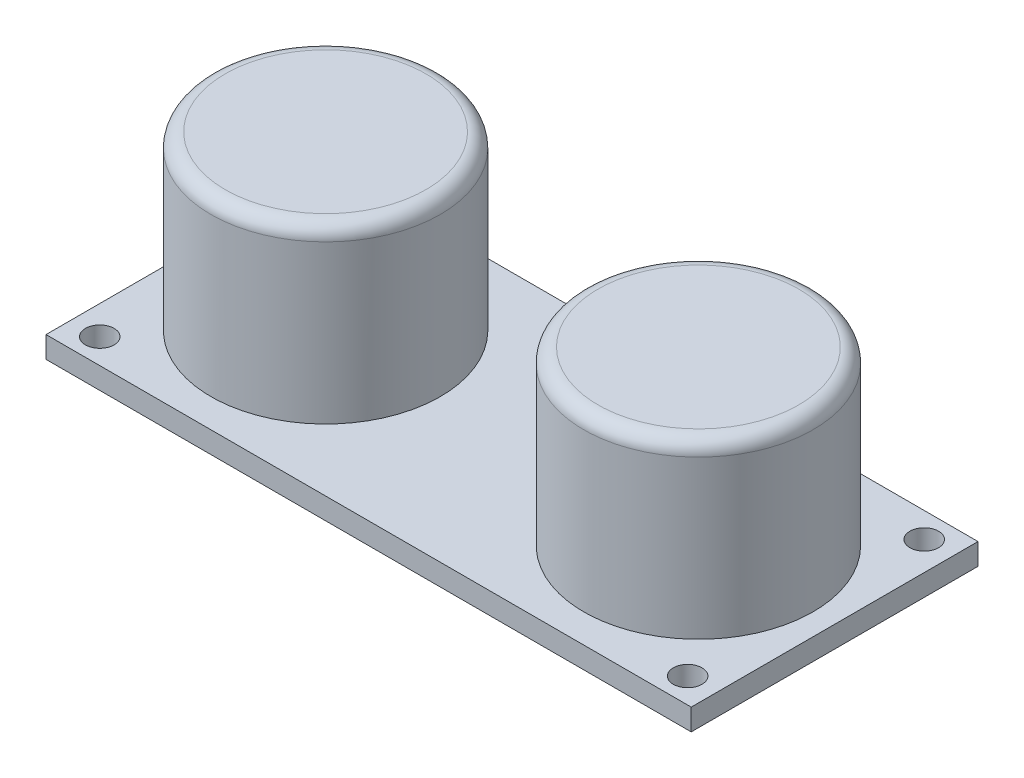
SolidWorks part; units mm, degrees
ref_plane "Front Plane" through (0, 0, 0) normal (0, 0, 1) x (1, 0, 0)
ref_plane "Top Plane" through (0, 0, 0) normal (0, 1, 0) x (1, 0, 0)
ref_plane "Right Plane" through (0, 0, 0) normal (1, 0, 0) x (0, 0, -1)
sketch "Sketch1" plane through (0, 0, 0) normal (0, 1, 0) x (1, 0, 0)
  line L0 (22.5, 20) -> (22.5, 0) construction
  line L1 (0, 0) -> (45, 0)
  line L2 (0, 0) -> (0, 20)
  line L3 (0, 20) -> (45, 20)
  line L4 (45, 0) -> (45, 20)
  line L6 (2, 1.75) -> (43, 1.75) construction
  line L7 (2, 1.75) -> (2, 18.25) construction
  line L8 (2, 18.25) -> (43, 18.25) construction
  line L9 (43, 1.75) -> (43, 18.25) construction
  line L10 (2, 1.75) -> (43, 18.25) construction
  line L11 (2, 18.25) -> (43, 1.75) construction
  circle A0 centre (2, 18.25) radius 1
  circle A1 centre (2, 1.75) radius 1
  circle A2 centre (43, 1.75) radius 1
  circle A3 centre (43, 18.25) radius 1
  point P7 (22.5, 10)
  dimension "D5" = 2
  dimension "D6" = 2
  dimension "D1" = 20
  dimension "D2" = 45
  dimension "D3" = 16.5
  dimension "D4" = 41
extrude "Boss-Extrude1" add sketch "Sketch1" along normal blind 1.5
sketch "Sketch2" plane through (0, 1.5, 0) normal (0, 1, 0) x (1, 0, 0)
  line L0 (0, 10) -> (45, 10) construction
  line L1 (0, 20) -> (0, 0) construction
  line L2 (45, 0) -> (45, 20) construction
  line L3 (22.5, 20) -> (22.5, 0) construction
  line L4 (45, 20) -> (0, 20) construction
  line L5 (0, 0) -> (45, 0) construction
  circle A0 centre (9.5, 10) radius 8
  circle A2 centre (35.5, 10) radius 8
  dimension "D1" = 13
  dimension "D2" = 16
extrude "Boss-Extrude2" add sketch "Sketch2" along normal blind 12
fillet "Fillet1" radius 1 2 edges at (9.5, 13.5, -2) (35.5, 13.5, -18)
